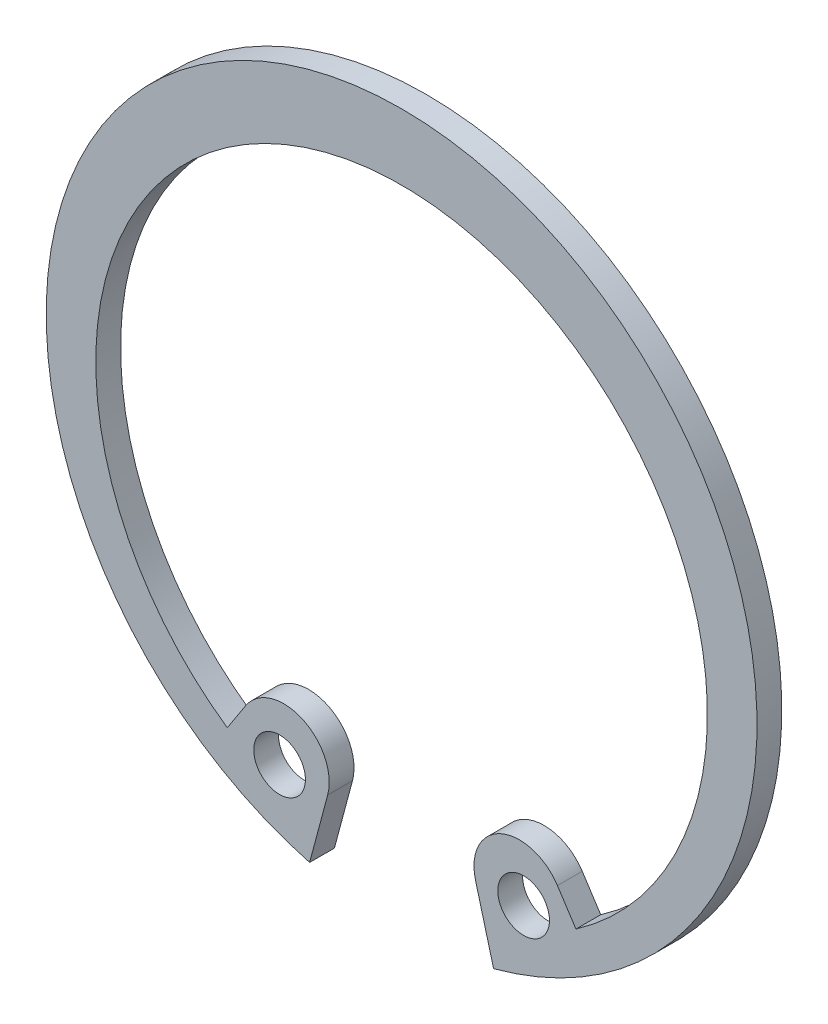
SolidWorks part; units mm, degrees
material "ASTM A36 Steel"
ref_plane "Front" through (0, 0, 0) normal (0, 0, 1) x (1, 0, 0)
ref_plane "Top" through (0, 0, 0) normal (0, 1, 0) x (1, 0, 0)
ref_plane "Right" through (0, 0, 0) normal (1, 0, 0) x (0, 0, -1)
sketch "Layout" plane through (0, 0, 0) normal (0, 0, 1) x (1, 0, 0)
  line L0 (0, 0) -> (4.4517, -16.6139) construction
  line L1 (0, 0) -> (0, -2.175) construction
  line L2 (0, 0) -> (9.3836, -14.4148) construction
  line L3 (0, 17.2) -> (0, 15.6) construction
  line L4 (0, -17.2) -> (0, -15.6) construction
  line L5 (0, 15.6) -> (0, 14) construction
  line L6 (4.8054, -10.7772) -> (0, 0) construction
  line L7 (4.8054, -10.7772) -> (7.0045, -15.7091) construction
  line L8 (-17.2, 0) -> (-16, 0) construction
  line L9 (3.0924, -11.541) -> (3.5613, -13.2909) construction
  line L10 (3.5613, -13.2909) -> (4.0301, -15.0407) construction
  line L11 (9.3836, -14.4148) -> (4.4517, -16.6139) construction
  line L12 (3.0924, -11.541) -> (6.5184, -10.0134) construction
  circle A0 centre (0, 0) radius 17.2 construction
  circle A1 centre (0, -0.8) radius 14.8 construction
  circle A3 centre (5.905, -13.2432) radius 1.25 construction
  dimension "D1" = 15
sketch "Sketch2" plane through (0, 0, 0) normal (0, 0, 1) x (1, 0, 0)
  line L0 (0, 0) -> (9.3836, -14.4148) construction
  line L1 (0, 0) -> (4.4517, -16.6139) construction
  line L2 (6.5184, -10.0134) -> (8.4365, -12.96)
  line L3 (3.0924, -11.541) -> (4.4517, -16.6139)
  line L4 (0, 0) -> (0, -2.175) construction
  line L5 (0, 7.7639) -> (0, -6.0981) construction
  line L6 (0, 17.2) -> (0, 14)
  line L7 (3.0924, -11.541) -> (6.5184, -10.0134) construction
  line L8 (3.0924, -11.541) -> (6.5184, -10.0134)
  circle A0 centre (0, -0.8) radius 14.8 construction
  arc A1 (8.4365, -12.96) -> (0, 14) centre (0, -0.8) ccw
  circle A2 centre (0, 0) radius 17.2 construction
  circle A3 centre (5.905, -13.2432) radius 1.25 construction
  arc A4 (4.4517, -16.6139) -> (0, 17.2) centre (0, 0) ccw
  circle A7 centre (5.905, -13.2432) radius 1.25
extrude "Boss-Extrude1" add sketch "Sketch2" along normal blind 1.2
fillet "Fillet1" radius 2.1972 4 edges at (6.5184, -10.0134, 0.6) (3.0924, -11.541, 0.6) (4.8054, -10.7772, 1.2) (4.8054, -10.7772, 0)
mirror "Mirror1" about plane through (0, 17.2, 1.2) normal (1, 0, 0) of bodies 109
equation "\"D1@Boss-Extrude1\"=\"thickness@Layout\""
